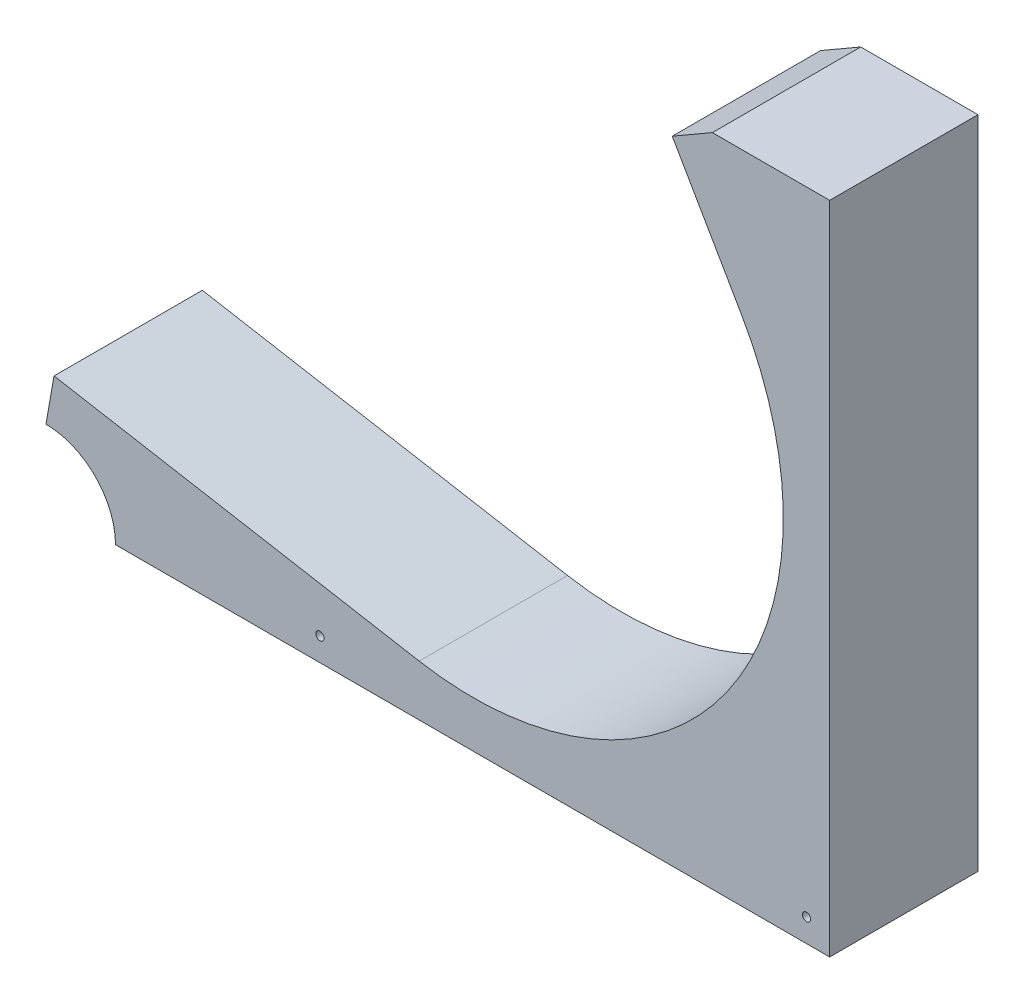
SolidWorks part; units mm, degrees
ref_plane "Front Plane" through (0, 0, 0) normal (0, 0, 1) x (1, 0, 0)
ref_plane "Top Plane" through (0, 0, 0) normal (0, 1, 0) x (1, 0, 0)
ref_plane "Right Plane" through (0, 0, 0) normal (1, 0, 0) x (0, 0, -1)
sketch "Sketch2" plane through (0, 0, 0) normal (0, 0, 1) x (1, 0, 0)
  line L0 (0, 0) -> (75.2886, 0)
  line L1 (75.2886, 0) -> (56.4664, 32.6009)
  line L2 (0, -65.2018) -> (-81.9123, -65.2018) construction
  line L3 (-11.3222, -64.2112) -> (-111.3786, -46.5686)
  line L4 (56.4664, 32.6009) -> (37.4164, 65.5965)
  arc A0 (56.4664, 32.6009) -> (-11.3222, -64.2112) centre (0, 0) cw
  circle A1 centre (0, 0) radius 45.212 construction
  point P11 (-11.3222, -64.2112)
  dimension "D3" = 90.424
  dimension "D1" = 65.2018
  dimension "D2" = 60
  dimension "D4" = 10
  dimension "D5" = 38.1
  dimension "D6" = 101.6
sketch3d "3DSketch1"
  line L0 (-114.819, -66.0796, 0) -> (-111.3786, -46.5686, 0) construction
  line L1 (-117.0243, -78.5867, -20.32) -> (-114.819, -66.0796, -20.32)
  line L2 (-117.0243, -78.5867, -20.32) -> (-117.0243, -78.5867, 20.32)
  line L3 (-117.0243, -78.5867, 20.32) -> (-114.819, -66.0796, 20.32)
  line L4 (-114.819, -66.0796, -20.32) -> (-114.819, -66.0796, 20.32)
  line L5 (-117.0243, -78.5867, -20.32) -> (-114.819, -66.0796, 20.32) construction
  line L6 (-117.0243, -78.5867, 20.32) -> (-114.819, -66.0796, -20.32) construction
  line L7 (-11.3222, -64.2112, 0) -> (-111.3786, -46.5686, 0) construction
  line L8 (0, -65.2018, 0) -> (-81.9123, -65.2018, 0) construction
  point P4 (-115.9216, -72.3331, 0)
  dimension "D1" = 12.7
  dimension "D2" = 40.64
  dimension "D3" = 19.812
sweep "Sweep3" add profiles "3DSketch1" path "Sketch2"
sketch "Sketch5" plane through (0, 0, 20.32) normal (0, 0, 1) x (1, 0, 0)
  line L0 (-117.0243, -78.5867) -> (-117.0243, -97.7138)
  line L1 (-117.0243, -97.7138) -> (97.7138, -97.7138)
  line L2 (97.7138, -97.7138) -> (97.7138, 81.8525)
  line L3 (97.7138, 81.8525) -> (65.5726, 81.8525)
  line L4 (-117.0243, -78.5867) -> (-16.9678, -96.2293)
  line L5 (84.6226, 48.8569) -> (65.5726, 81.8525)
  arc A0 (-16.9678, -96.2293) -> (84.6226, 48.8569) centre (0, 0) ccw construction
  arc A1 (-16.9678, -96.2293) -> (84.6226, 48.8569) centre (0, 0) ccw
  line M7 (-117.0243, -78.5867) -> (-16.9678, -96.2293)
extrude "Boss-Extrude1" add sketch "Sketch5" against normal up to surface (40.64 mm away) contours A1 L0 L1 M7 | A1 L1 L2 | A1 L2 L3 L5 up to face at (-65.8934, -81.1545, -20.32)
sketch "Sketch6" plane through (0, 0, 20.32) normal (0, 0, 1) x (1, 0, 0)
  circle A0 centre (91.3638, -91.3638) radius 1.1303 construction
  circle A1 centre (-41.9735, -91.3638) radius 1.1303 construction
  circle A2 centre (91.3638, -91.3638) radius 1.1303
  circle A3 centre (-41.9735, -91.3638) radius 1.1303
extrude "Cut-Extrude1" cut sketch "Sketch6" against normal through all
sketch "Sketch7" plane through (0, 0, 20.32) normal (0, 0, 1) x (1, 0, 0)
  circle A0 centre (-117.0243, -97.7138) radius 19.05
  dimension "D1" = 38.1
extrude "Cut-Extrude2" cut sketch "Sketch7" against normal through all
